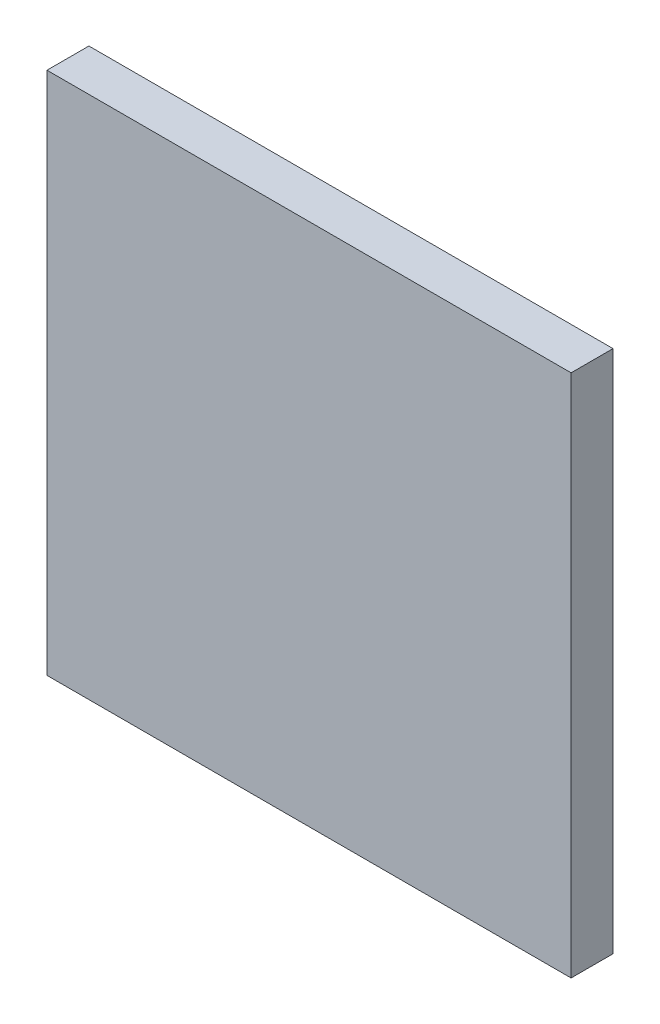
SolidWorks part; units mm, degrees
material "Thermal-Paste"
ref_plane "Ön Düzlem" through (0, 0, 0) normal (0, 0, 1) x (1, 0, 0)
ref_plane "Üst Düzlem" through (0, 0, 0) normal (0, 1, 0) x (1, 0, 0)
ref_plane "Sağ Düzlem" through (0, 0, 0) normal (1, 0, 0) x (0, 0, -1)
sketch "Sketch1" plane through (0, 0, 0) normal (0, 0, 1) x (1, 0, 0)
  line L1 (0, 0) -> (25, 0)
  line L2 (0, 0) -> (0, 25)
  line L3 (0, 25) -> (25, 25)
  line L4 (25, 0) -> (25, 25)
  dimension "D1" = 25
  dimension "D2" = 25
extrude "Boss-Extrude1" add sketch "Sketch1" along normal blind 2 contours L2 L1 L4 L3
